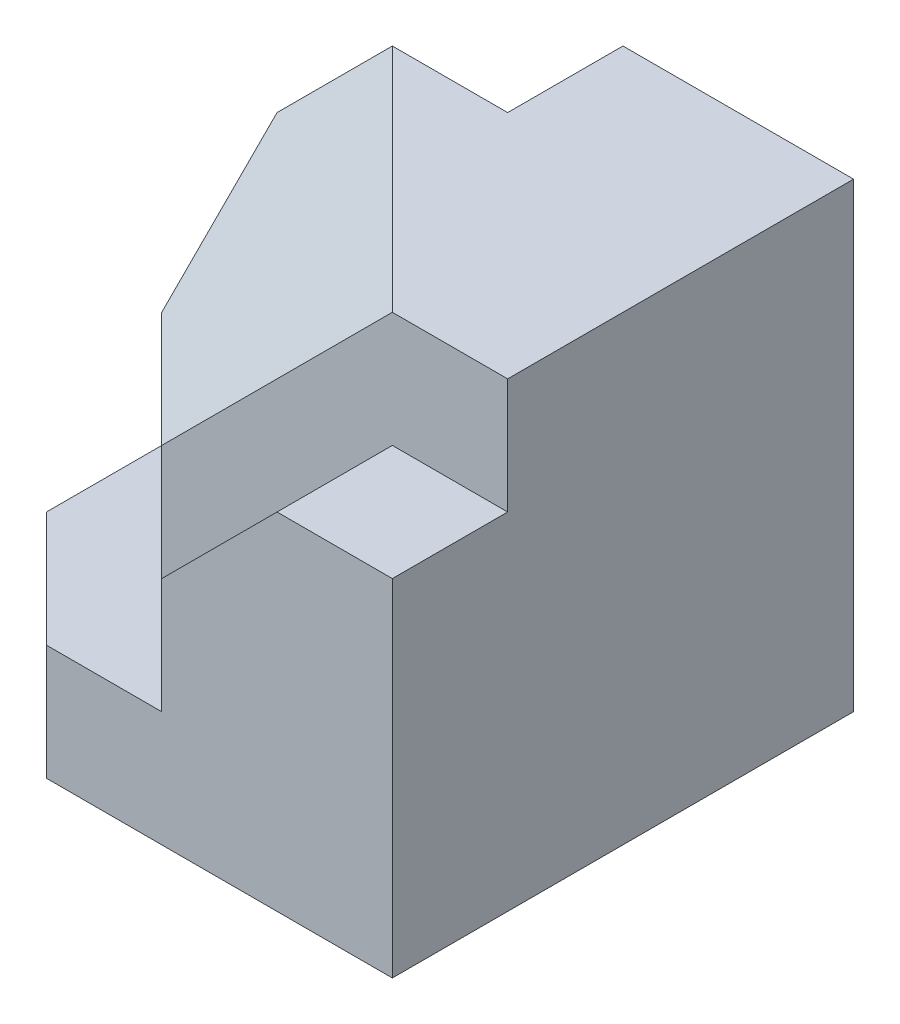
SolidWorks part; units mm, degrees
ref_plane "Front Plane" through (0, 0, 0) normal (0, 0, 1) x (1, 0, 0)
ref_plane "Top Plane" through (0, 0, 0) normal (0, 1, 0) x (1, 0, 0)
ref_plane "Right Plane" through (0, 0, 0) normal (1, 0, 0) x (0, 0, -1)
sketch "Sketch2" plane through (0, 0, 0) normal (0, 1, 0) x (1, 0, 0)
  line L0 (-10, -5) -> (-10, 0)
  line L1 (-10, 0) -> (0, 0)
  line L2 (0, 0) -> (0, -15)
  line L3 (0, -15) -> (-5, -15)
  line L4 (-5, -15) -> (-15, -5)
  line L5 (-15, -5) -> (-10, -5)
  dimension "D1" = 10
  dimension "D2" = 15
  dimension "D3" = 5
  dimension "D4" = 5
  dimension "D5" = 5
extrude "Boss-Extrude1" add sketch "Sketch2" along normal blind 20
ref_plane "Plane1" through (0, 0, 0) normal (0, -1, 0) x (-1, 0, 0)
sketch "Sketch3" plane through (0, 0, 0) normal (0, -1, 0) x (-1, 0, 0)
  line L0 (15, -5) -> (5, -15)
  line L1 (5, -15) -> (15, -15)
  line L2 (15, -15) -> (20, -10)
  line L3 (20, -10) -> (20, -5)
  line L4 (20, -5) -> (15, -5)
  dimension "D1" = 10
  dimension "D2" = 5
  dimension "D3" = 5
extrude "Boss-Extrude2" add sketch "Sketch3" against normal blind 20
sketch3d "3DSketch2"
  line L0 (-10, 20, 5) -> (-20, 20, 5) construction
  line L1 (-20, 20, 5) -> (-20, 0, 5) construction
  line L2 (-20, 20, 10) -> (-20, 0, 10) construction
  line L3 (-15, 20, 15) -> (-15, 0, 15) construction
  line L4 (-15, 20, 15) -> (0, 20, 15) construction
  line L5 (0, 20, 15) -> (0, 0, 15) construction
  line L6 (-15, 20, 15) -> (-20, 20, 10) construction
  line L7 (-20, 20, 10) -> (-20, 20, 5) construction
  line L8 (-15, 20, 5) -> (-5, 20, 15)
  line L9 (-5, 20, 15) -> (-15, 10, 15)
  line L10 (-15, 10, 15) -> (-20, 10, 10)
  line L11 (-20, 10, 10) -> (-20, 15, 5)
  line L12 (-20, 15, 5) -> (-15, 20, 5)
  point P0 (-15, 20, 5)
  point P1 (-20, 15, 5)
  point P4 (-20, 10, 10)
  point P7 (-15, 10, 15)
  point P10 (-5, 20, 15)
  dimension "D1" = 5
  dimension "D2" = 10
  dimension "D3" = 10
  dimension "D4" = 5
extrude "Cut-Extrude1" cut sketch "3DSketch2" along direction (0, 1, 0) on the side of the normal blind 20
sketch "Sketch5" plane through (0, 0, 15) normal (0, 0, 1) x (1, 0, 0)
  line L0 (0, 15) -> (-5, 15)
  line L1 (0, 20) -> (0, 0) construction
  line L2 (-5, 15) -> (-10, 10)
  line L3 (-10, 10) -> (-10, 5)
  line L4 (-15, 0) -> (0, 0) construction
  line L5 (-15, 0) -> (0, 0)
  line L6 (0, 0) -> (0, 15)
  line L7 (-10, 5) -> (-15, 5)
  line L8 (-15, 5) -> (-15, 0)
  line L9 (-15, 0) -> (-20, 0) construction
  dimension "D1" = 15
  dimension "D2" = 5
  dimension "D3" = 5
  dimension "D4" = 5
  dimension "D5" = 5
  dimension "D6" = 15
extrude "Boss-Extrude3" add sketch "Sketch5" along normal blind 5
sketch "Sketch6" plane through (0, 0, 0) normal (0, -1, 0) x (-1, 0, 0)
  line L0 (20, -10) -> (15, -15)
  line L1 (15, -15) -> (15, -20)
  line L2 (15, -20) -> (20, -15)
  line L3 (20, -15) -> (20, -10)
extrude "Boss-Extrude4" add sketch "Sketch6" against normal blind 5
sketch "Sketch7" plane through (-10, 0, 0) normal (-1, 0, 0) x (0, 0, 1)
  line L1 (0, 0) -> (5, 0)
  line L2 (0, 0) -> (0, 15)
  line L3 (0, 15) -> (5, 15)
  line L4 (5, 0) -> (5, 15)
extrude "Boss-Extrude5" add sketch "Sketch7" along normal blind 10
